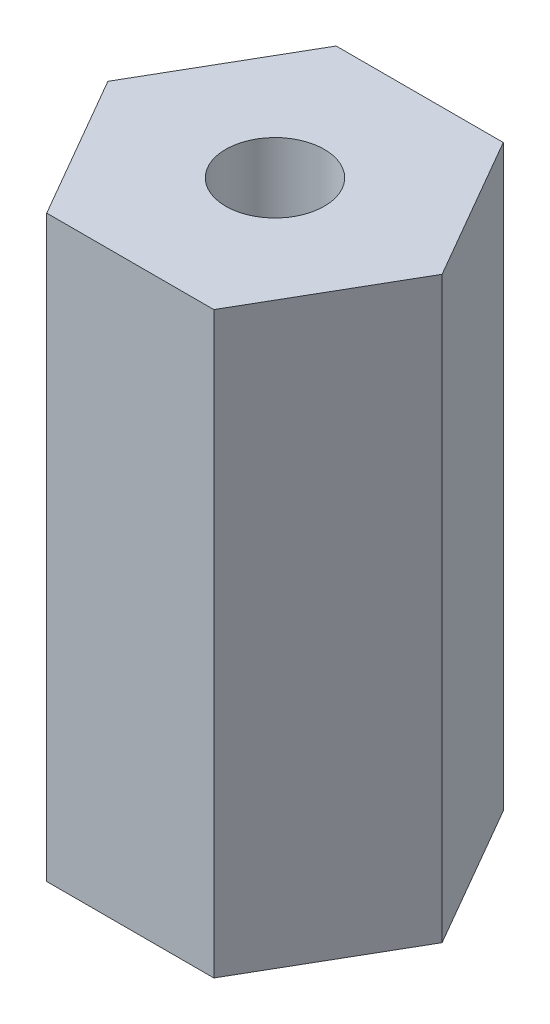
SolidWorks part; units mm, degrees
material "Copper"
ref_plane "Front Plane" through (0, 0, 0) normal (0, 0, 1) x (1, 0, 0)
ref_plane "Top Plane" through (0, 0, 0) normal (0, 1, 0) x (1, 0, 0)
ref_plane "Right Plane" through (0, 0, 0) normal (1, 0, 0) x (0, 0, -1)
sketch "Sketch2" plane through (0, 0, 0) normal (0, 1, 0) x (1, 0, 0)
  line L1 (4.5827, 0) -> (2.2914, 3.9688)
  line L2 (2.2914, 3.9688) -> (-2.2914, 3.9687)
  line L3 (-2.2914, 3.9687) -> (-4.5827, 0)
  line L4 (-4.5827, 0) -> (-2.2914, -3.9688)
  line L5 (-2.2914, -3.9688) -> (2.2914, -3.9687)
  line L6 (2.2914, -3.9687) -> (4.5827, 0)
  circle A0 centre (0, 0) radius 3.9688 construction
  dimension "D1" = 7.9375
extrude "Boss-Extrude1" add sketch "Sketch2" along normal blind 15.875
hole_wizard "#6-32 Tapped Hole1" positions "Sketch4" profile "Sketch3" tap size "#6-32" standard "ANSI Inch"
sketch "Sketch4" plane through (0, 0, 0) normal (0, -1, 0) x (-1, 0, 0)
  point P0 (0, 0)
sketch "Sketch3" plane through (0, 0, 0) normal (1, 0, 0) x (0, 0, -1)
  line L0 (0, 0) -> (0, 5.8927)
  line L1 (0, 5.8927) -> (1.3525, 5.08)
  line L2 (1.3525, 5.08) -> (1.3525, 0)
  line L5 (1.3525, 0) -> (0, 0)
  line L10 (0, 5.8927) -> (-1.3526, 5.08) construction
  line L11 (0, -6.35) -> (0, 107.95) construction
  dimension "Tap Drill Dia." = 2.7051
  dimension "Tap Drill Depth" = 5.08
  dimension "Drill Angle" = 118
cosmetic thread "Hole Thread1" parameters "D1"=3.9688, "D2"=3.5052
hole_wizard "#6-32 Tapped Hole2" positions "Sketch6" profile "Sketch5" tap size "#6-32" standard "ANSI Inch"
sketch "Sketch6" plane through (0, 15.875, 0) normal (0, 1, 0) x (1, 0, 0)
  point P0 (0, 0)
sketch "Sketch5" plane through (0, 15.875, 0) normal (1, 0, 0) x (0, 0, 1)
  line L0 (0, 0) -> (0, 5.8927)
  line L1 (0, 5.8927) -> (1.3525, 5.08)
  line L2 (1.3525, 5.08) -> (1.3525, 0)
  line L5 (1.3525, 0) -> (0, 0)
  line L10 (0, 5.8927) -> (-1.3526, 5.08) construction
  line L11 (0, -6.35) -> (0, 107.95) construction
  dimension "Tap Drill Dia." = 2.7051
  dimension "Tap Drill Depth" = 5.08
  dimension "Drill Angle" = 118
cosmetic thread "Hole Thread2" parameters "D1"=4.064, "D2"=3.5052
